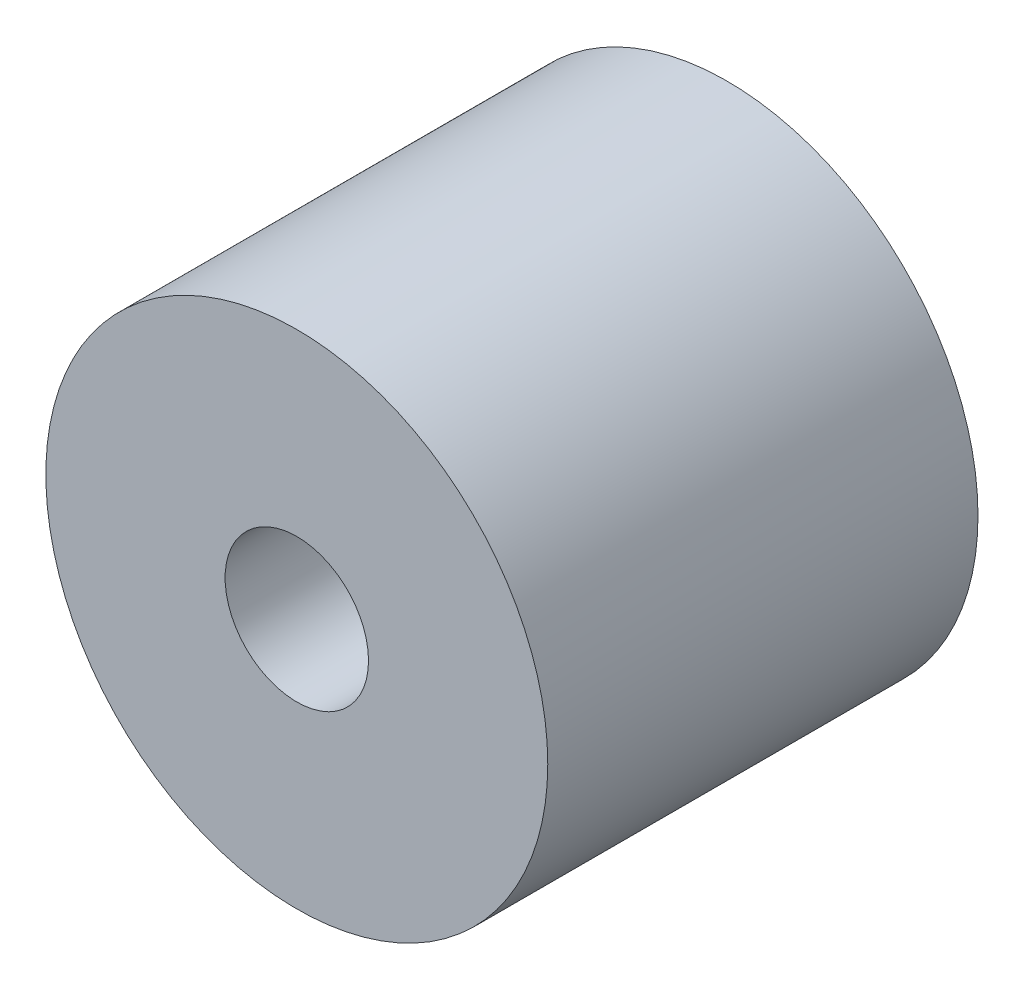
SolidWorks part; units mm, degrees
ref_plane "Alzado" through (0, 0, 0) normal (0, 0, 1) x (1, 0, 0)
ref_plane "Planta" through (0, 0, 0) normal (0, 1, 0) x (1, 0, 0)
ref_plane "Vista lateral" through (0, 0, 0) normal (1, 0, 0) x (0, 0, -1)
sketch "Croquis1" plane through (0, 0, 0) normal (0, 0, 1) x (1, 0, 0)
  circle A0 centre (0, 0) radius 17.5
  circle A1 centre (0, 0) radius 5
  dimension "D1" = 35
  dimension "D2" = 10
extrude "Saliente-Extruir1" add sketch "Croquis1" along normal mid plane 30
